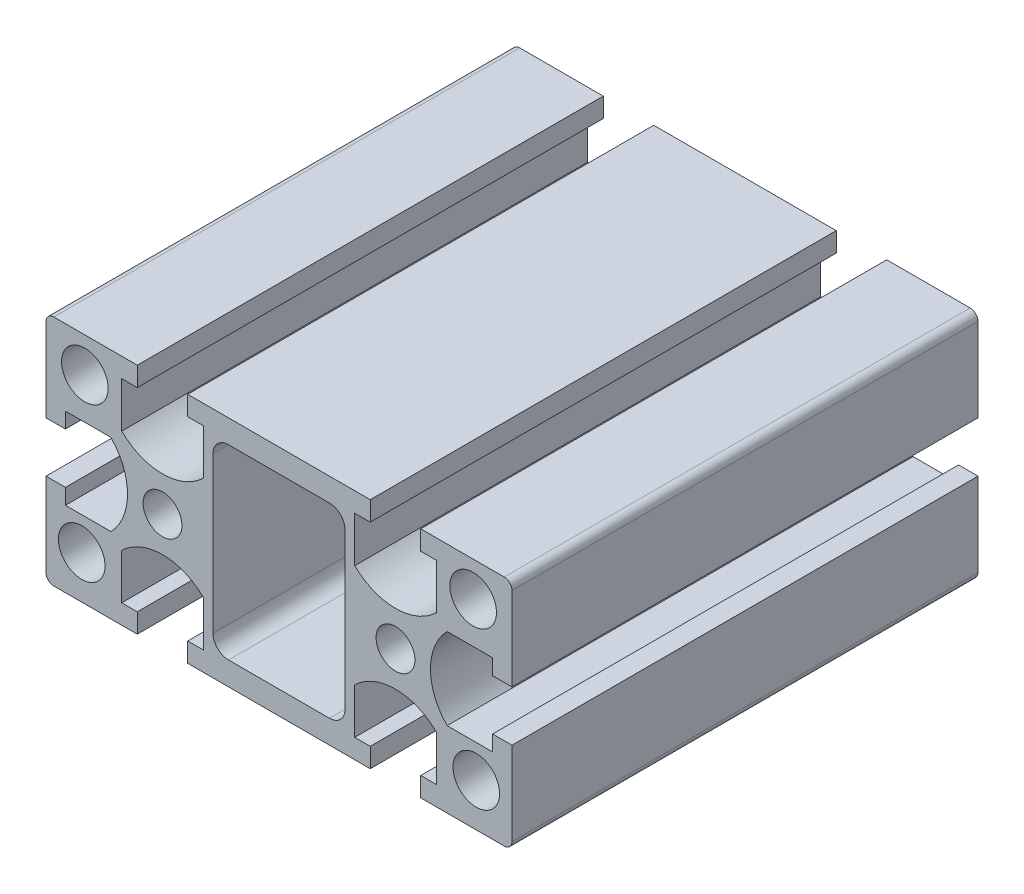
SolidWorks part; units mm, degrees
ref_plane "Front Plane" through (0, 0, 0) normal (0, 0, 1) x (1, 0, 0)
ref_plane "Top Plane" through (0, 0, 0) normal (0, 1, 0) x (1, 0, 0)
ref_plane "Right Plane" through (0, 0, 0) normal (1, 0, 0) x (0, 0, -1)
sketch "Model" plane through (0, 0, 0) normal (0, 0, 1) x (1, 0, 0)
  line L0 (6.5, 12) -> (-6.5, 12)
  line L1 (8.5, 10) -> (8.5, -10)
  line L2 (6.5, -12) -> (-6.5, -12)
  line L3 (-8.5, 10) -> (-8.5, -10)
  line L4 (-27.5, 3.25) -> (-30, 3.25)
  line L5 (-30, -3.25) -> (-27.5, -3.25)
  line L6 (-21.6439, 5.25) -> (-27.5, 5.25)
  line L7 (-27.5, 5.25) -> (-27.5, 3.25)
  line L8 (-21.6439, -5.25) -> (-27.5, -5.25)
  line L9 (-27.5, -5.25) -> (-27.5, -3.25)
  line L10 (-18.25, 15) -> (-18.25, 12.5)
  line L11 (-20.25, 12.5) -> (-18.25, 12.5)
  line L12 (-20.25, 6.6439) -> (-20.25, 12.5)
  line L13 (-9.75, 6.6439) -> (-9.75, 12.5)
  line L14 (-9.75, 12.5) -> (-11.75, 12.5)
  line L15 (-11.75, 12.5) -> (-11.75, 15)
  line L16 (-11.75, -15) -> (-11.75, -12.5)
  line L17 (-9.75, -12.5) -> (-11.75, -12.5)
  line L18 (-9.75, -6.6439) -> (-9.75, -12.5)
  line L19 (-20.25, -6.6439) -> (-20.25, -12.5)
  line L20 (-20.25, -12.5) -> (-18.25, -12.5)
  line L21 (-18.25, -12.5) -> (-18.25, -15)
  line L22 (18.25, -12.5) -> (18.25, -15)
  line L23 (20.25, -12.5) -> (18.25, -12.5)
  line L24 (20.25, -6.6439) -> (20.25, -12.5)
  line L25 (9.75, -6.6439) -> (9.75, -12.5)
  line L26 (9.75, -12.5) -> (11.75, -12.5)
  line L27 (11.75, -15) -> (11.75, -12.5)
  line L28 (27.5, 3.25) -> (30, 3.25)
  line L29 (27.5, 5.25) -> (27.5, 3.25)
  line L30 (21.6439, 5.25) -> (27.5, 5.25)
  line L31 (21.6439, -5.25) -> (27.5, -5.25)
  line L32 (27.5, -5.25) -> (27.5, -3.25)
  line L33 (30, -3.25) -> (27.5, -3.25)
  line L34 (11.75, 12.5) -> (11.75, 15)
  line L35 (9.75, 12.5) -> (11.75, 12.5)
  line L36 (9.75, 6.6439) -> (9.75, 12.5)
  line L37 (20.25, 6.6439) -> (20.25, 12.5)
  line L38 (20.25, 12.5) -> (18.25, 12.5)
  line L39 (18.25, 15) -> (18.25, 12.5)
  line L40 (-18.25, 15) -> (-29, 15)
  line L41 (-30, 14) -> (-30, 3.25)
  line L42 (-30, -3.25) -> (-30, -14)
  line L43 (-29, -15) -> (-18.25, -15)
  line L44 (-11.75, -15) -> (11.75, -15)
  line L45 (18.25, -15) -> (29, -15)
  line L46 (30, -14) -> (30, -3.25)
  line L47 (30, 3.25) -> (30, 14)
  line L48 (29, 15) -> (18.25, 15)
  line L49 (11.75, 15) -> (-11.75, 15)
  circle A0 centre (-15, 0) radius 2.5
  circle A1 centre (-25, 10.5314) radius 3
  circle A2 centre (-25.3993, -9.4686) radius 3
  arc A3 (-21.6439, -5.25) -> (-21.6439, 5.25) centre (-27, 0) ccw
  arc A4 (-20.25, 6.6439) -> (-9.75, 6.6439) centre (-15, 12) ccw
  arc A5 (-9.75, -6.6439) -> (-20.25, -6.6439) centre (-15, -12) ccw
  circle A6 centre (25.3993, -9.4686) radius 3
  arc A7 (20.25, -6.6439) -> (9.75, -6.6439) centre (15, -12) ccw
  circle A8 centre (15, 0) radius 2.5
  arc A9 (21.6439, 5.25) -> (21.6439, -5.25) centre (27, 0) ccw
  circle A10 centre (25, 10.5314) radius 3
  arc A11 (9.75, 6.6439) -> (20.25, 6.6439) centre (15, 12) ccw
  arc A12 (30, 14) -> (29, 15) centre (29, 14) ccw
  arc A13 (29, -15) -> (30, -14) centre (29, -14) ccw
  arc A14 (-30, -14) -> (-29, -15) centre (-29, -14) ccw
  arc A15 (-29, 15) -> (-30, 14) centre (-29, 14) ccw
  arc A16 (-8.5, -10) -> (-6.5, -12) centre (-6.5, -10) ccw
  arc A17 (6.5, -12) -> (8.5, -10) centre (6.5, -10) ccw
  arc A18 (8.5, 10) -> (6.5, 12) centre (6.5, 10) ccw
  arc A19 (-6.5, 12) -> (-8.5, 10) centre (-6.5, 10) ccw
  point P90 (0, 0)
  point P91 (0, 0)
extrude "Boss-Extrude1" add sketch "Model" along normal blind 60
